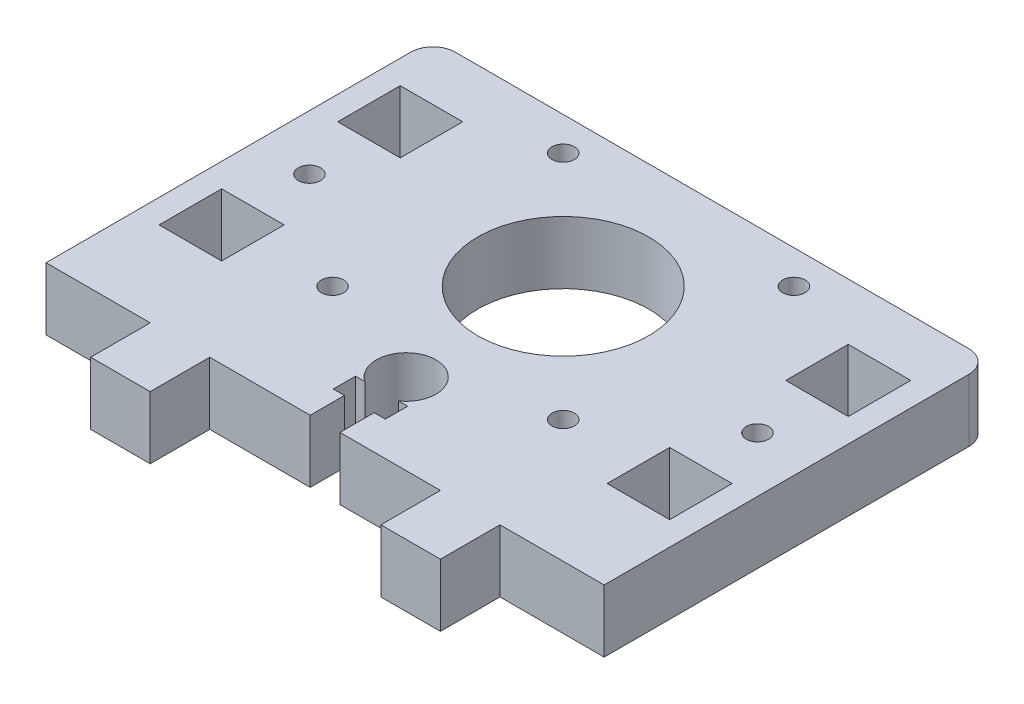
SolidWorks part; units mm, degrees
ref_plane "Front Plane" through (0, 0, 0) normal (0, 0, 1) x (1, 0, 0)
ref_plane "Top Plane" through (0, 0, 0) normal (0, 1, 0) x (1, 0, 0)
ref_plane "Right Plane" through (0, 0, 0) normal (1, 0, 0) x (0, 0, -1)
sketch "Sketch1" plane through (0, 0, 0) normal (0, 1, 0) x (1, 0, 0)
  line L0 (0, 26) -> (0, -26) construction
  line L1 (-34.5, 26) -> (34.5, 26)
  line L2 (-37.5, 23) -> (-37.5, -26)
  line L3 (-37.5, -26) -> (-23.5, -26)
  line L4 (37.5, 23) -> (37.5, -26)
  line L5 (-37.5, 26) -> (37.5, -26) construction
  line L6 (-37.5, -26) -> (37.5, 26) construction
  line L7 (-11.5, 6) -> (11.5, 6) construction
  line L8 (0, 6) -> (15.5, 21.5) construction
  line L9 (-30.1, 26) -> (-30.1, -26) construction
  line L10 (-37.5, 2.2) -> (37.5, 2.2) construction
  line L11 (-34.3, 18.4) -> (-25.9, 18.4)
  line L12 (-34.3, 18.4) -> (-34.3, 10)
  line L13 (-34.3, 10) -> (-25.9, 10)
  line L14 (-25.9, 18.4) -> (-25.9, 10)
  line L15 (-34.3, 18.4) -> (-25.9, 10) construction
  line L16 (-34.3, 10) -> (-25.9, 18.4) construction
  line L17 (-34.3, -5.6) -> (-25.9, -14) construction
  line L18 (-34.3, -14) -> (-25.9, -5.6) construction
  line L19 (-25.9, -14) -> (-25.9, -5.6)
  line L20 (-34.3, -5.6) -> (-25.9, -5.6)
  line L21 (-34.3, -14) -> (-34.3, -5.6)
  line L22 (-34.3, -14) -> (-25.9, -14)
  line L23 (34.3, -14) -> (25.9, -5.6) construction
  line L24 (34.3, -5.6) -> (25.9, -14) construction
  line L25 (34.3, 10) -> (25.9, 18.4) construction
  line L26 (34.3, 18.4) -> (25.9, 10) construction
  line L27 (34.3, -14) -> (25.9, -14)
  line L28 (34.3, -14) -> (34.3, -5.6)
  line L29 (34.3, -5.6) -> (25.9, -5.6)
  line L30 (25.9, -14) -> (25.9, -5.6)
  line L31 (25.9, 18.4) -> (25.9, 10)
  line L32 (34.3, 10) -> (25.9, 10)
  line L33 (34.3, 18.4) -> (34.3, 10)
  line L34 (34.3, 18.4) -> (25.9, 18.4)
  line L35 (-2, -26) -> (-2, -21.4)
  line L36 (-2, -21.4) -> (-3.5, -21.4)
  line L37 (-3.5, -21.4) -> (-3.5, -18.4)
  line L38 (-3.5, -18.4) -> (-2.2605, -18.4)
  line L39 (3.5, -18.4) -> (2.2605, -18.4)
  line L40 (3.5, -21.4) -> (3.5, -18.4)
  line L41 (2, -21.4) -> (3.5, -21.4)
  line L42 (2, -26) -> (2, -21.4)
  line L43 (-19.5, -34) -> (-19.5, -26) construction
  line L44 (-15.5, -26) -> (-15.5, -34)
  line L45 (-15.5, -34) -> (-23.5, -34)
  line L46 (-23.5, -34) -> (-23.5, -26)
  line L47 (-15.5, -26) -> (-2, -26)
  line L48 (15.5, -26) -> (2, -26)
  line L49 (23.5, -34) -> (23.5, -26)
  line L50 (15.5, -34) -> (23.5, -34)
  line L51 (15.5, -26) -> (15.5, -34)
  line L52 (19.5, -34) -> (19.5, -26) construction
  line L53 (23.5, -26) -> (37.5, -26)
  arc A0 (34.5, 26) -> (37.5, 23) centre (34.5, 23) cw
  arc A1 (-34.5, 26) -> (-37.5, 23) centre (-34.5, 23) ccw
  circle A2 centre (0, 6) radius 11.5
  circle A3 centre (15.5, 21.5) radius 1.5
  circle A4 centre (-15.5, 21.5) radius 1.5
  circle A5 centre (15.5, -9.5) radius 1.5
  circle A6 centre (-15.5, -9.5) radius 1.5
  circle A7 centre (-30.1, 2) radius 1.5
  circle A8 centre (30.1, 2) radius 1.5
  arc A9 (2.2605, -18.4) -> (-2.2605, -18.4) centre (0, -15.1) ccw
  point P0 (0, 0)
  point P28 (-30.1, 14.2)
  point P39 (-30.1, -9.8)
  point P48 (30.1, -9.8)
  point P49 (30.1, 14.2)
  dimension "D3" = 3
  dimension "D4" = 3
  dimension "D7" = 23
  dimension "D15" = 3
  dimension "D16" = 4
  dimension "D18" = 3.3
  dimension "D1" = 52
  dimension "D2" = 75
  dimension "D5" = 15.5
  dimension "D6" = 45
  dimension "D8" = 20
  dimension "D9" = 8.4
  dimension "D10" = 8.4
  dimension "D11" = 7.6
  dimension "D12" = 3.2
  dimension "D13" = 12
  dimension "D14" = 8
  dimension "D17" = 3
  dimension "D19" = 4.6
  dimension "D20" = 2
  dimension "D21" = 1.5
  dimension "D22" = 8
  dimension "D23" = 8
  dimension "D24" = 14
extrude "Boss-Extrude1" add sketch "Sketch1" along normal blind 8.4
